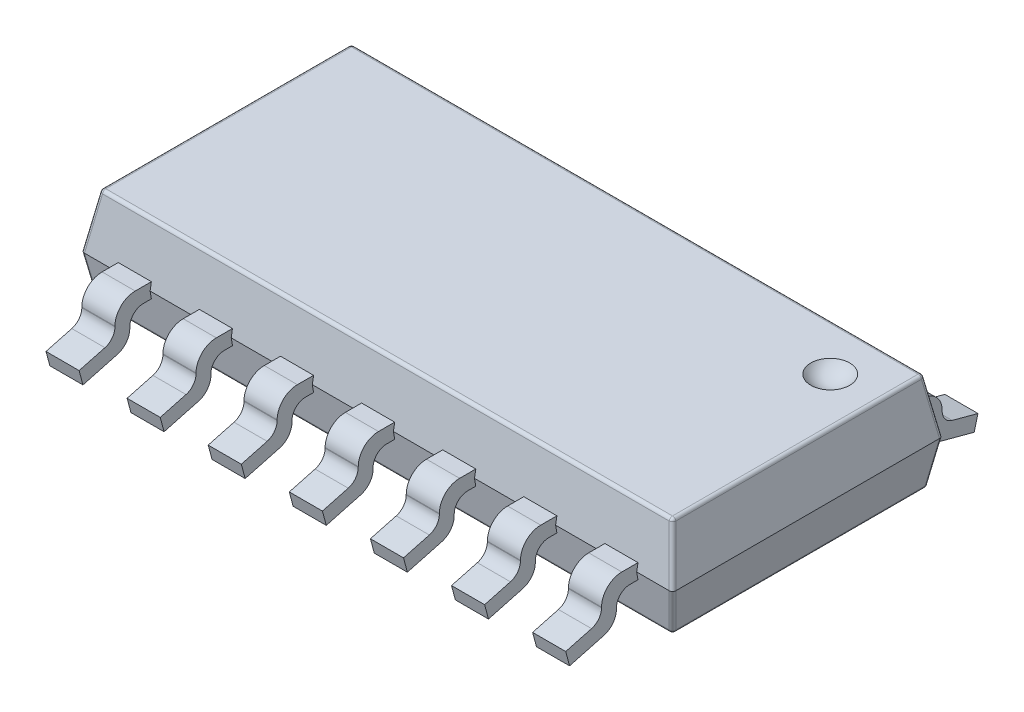
SolidWorks part; units mm, degrees
ref_plane "Front Plane" through (0, 0, 0) normal (0, 0, 1) x (1, 0, 0)
ref_plane "Top Plane" through (0, 0, 0) normal (0, 1, 0) x (1, 0, 0)
ref_plane "Right Plane" through (0, 0, 0) normal (1, 0, 0) x (0, 0, -1)
sketch "Sketch3" plane through (0, 0, 0) normal (1, 0, 0) x (0, 0, -1)
  line L0 (-2, 0) -> (2, 0) construction
  line L1 (-2, 0) -> (-1.8854, -0.65)
  line L2 (-1.8854, -0.65) -> (1.8854, -0.65)
  line L3 (1.8854, -0.65) -> (2, 0)
  line L4 (2, 0) -> (1.8589, 0.8)
  line L5 (1.8589, 0.8) -> (-1.8589, 0.8)
  line L6 (-1.8589, 0.8) -> (-2, 0)
  point P4 (0, 0)
  dimension "D1" = 4
  dimension "D2" = 1.45
  dimension "D3" = 0.65
  dimension "D4" = 100
  dimension "D5" = 100
  dimension "D6" = 100
  dimension "D7" = 100
extrude "Boss-Extrude1" add sketch "Sketch3" along normal mid plane 8.75
sketch "Sketch4" plane through (0, 0, 0) normal (0, 0, 1) x (1, 0, 0)
  line L0 (-4.375, 0) -> (-4.2339, 0.8)
  line L1 (4.375, 0.8) -> (-4.375, 0.8) construction
  line L2 (-4.2339, 0.8) -> (-4.7419, 0.8)
  line L3 (-4.375, 0) -> (-4.2604, -0.65)
  line L4 (4.375, -0.65) -> (-4.375, -0.65) construction
  line L5 (-4.2604, -0.65) -> (-4.7419, -0.65)
  line L6 (-4.7419, -0.65) -> (-4.7419, 0.8)
  line L7 (0, 0) -> (0, 1.6058) construction
  line L8 (4.7419, -0.65) -> (4.7419, 0.8)
  line L9 (4.2604, -0.65) -> (4.7419, -0.65)
  line L10 (4.375, 0) -> (4.2604, -0.65)
  line L11 (4.2339, 0.8) -> (4.7419, 0.8)
  line L12 (4.375, 0) -> (4.2339, 0.8)
  dimension "D1" = 80
  dimension "D2" = 80
extrude "Cut-Extrude1" cut sketch "Sketch4" against normal mid plane 8.75
fillet "Fillet1" radius 0.05 16 edges at (0, -0.65, -1.8854) (-4.2604, -0.65, 0) (0, -0.65, 1.8854) (-4.2339, 0.8, 0) (0, 0.8, -1.8589) (4.3177, -0.325, -1.9427) (4.3045, 0.4, -1.9295) (4.2339, 0.8, 0) (4.2604, -0.65, 0) (4.3177, -0.325, 1.9427) (4.3045, 0.4, 1.9295) (0, 0.8, 1.8589) (-4.3177, -0.325, 1.9427) (-4.3045, 0.4, 1.9295) (-4.3177, -0.325, -1.9427) (-4.3045, 0.4, -1.9295)
sketch "Sketch5" plane through (0, 0, 0) normal (1, 0, 0) x (0, 0, -1)
  line L0 (-1.9806, 0.11) -> (-2, 0)
  line L1 (-2, 0) -> (-1.8662, 0.7587) construction
  line L2 (-2, 0) -> (-1.9806, -0.11)
  line L3 (-1.8927, -0.6087) -> (-2, 0) construction
  line L4 (-1.9806, -0.11) -> (-2.1, -0.11)
  line L5 (-1.9806, 0.11) -> (-2.1807, 0.11)
  line L6 (-2, 0) -> (-2.2055, 0) construction
  line L7 (-2.3, -0.31) -> (-2.3, -0.3292)
  line L8 (-2.4853, -0.5707) -> (-2.9931, -0.7068)
  line L9 (-2.9931, -0.7068) -> (-3.05, -0.4943)
  line L10 (-3.05, -0.4943) -> (-2.6682, -0.392)
  line L11 (-2.52, -0.1988) -> (-2.52, -0.19)
  line L12 (-2.22, 0.11) -> (-2.1807, 0.11)
  arc A1 (-2.6682, -0.392) -> (-2.52, -0.1988) centre (-2.72, -0.1988) ccw
  arc A2 (-2.1, -0.11) -> (-2.3, -0.31) centre (-2.1, -0.31) ccw
  arc A4 (-2.52, -0.19) -> (-2.22, 0.11) centre (-2.22, -0.19) cw
  arc A5 (-2.4853, -0.5707) -> (-2.3, -0.3292) centre (-2.55, -0.3292) ccw
  dimension "D8" = 0.3
  dimension "D9" = 0.25
  dimension "D1" = 0.22
  dimension "D2" = 0.75
  dimension "D3" = 1.05
  dimension "D4" = 0.22
  dimension "D5" = 0.22
  dimension "D6" = 105
extrude "Boss-Extrude2" add sketch "Sketch5" along normal mid plane 0.49
pattern_linear "LPattern1" count 4 spacing 1.2 along (1, 0, 0) count 4 spacing 1.2 along (-1, 0, 0) of "Boss-Extrude2"
mirror "Mirror1" about plane through (0, 0, 0) normal (0, 0, 1) of "LPattern1", "Boss-Extrude2"
ref_plane "Plane1" through (0, 1, 0) normal (0, 1, 0) x (1, 0, 0)
sketch "Sketch6" plane through (0, 1, 0) normal (0, 1, 0) x (1, 0, 0)
  line L0 (4.192, 1.817) -> (-4.192, 1.817) construction
  line L1 (4.192, -1.817) -> (4.192, 1.817) construction
  line L2 (3.192, 1.167) -> (3.892, 1.167)
  arc A0 (3.892, 1.167) -> (3.192, 1.167) centre (3.542, 1.167) ccw
  dimension "D1" = 0.7
  dimension "D2" = 0.65
  dimension "D3" = 0.65
revolve "Cut-Revolve1" cut sketch "Sketch6" angle 360 about L2
